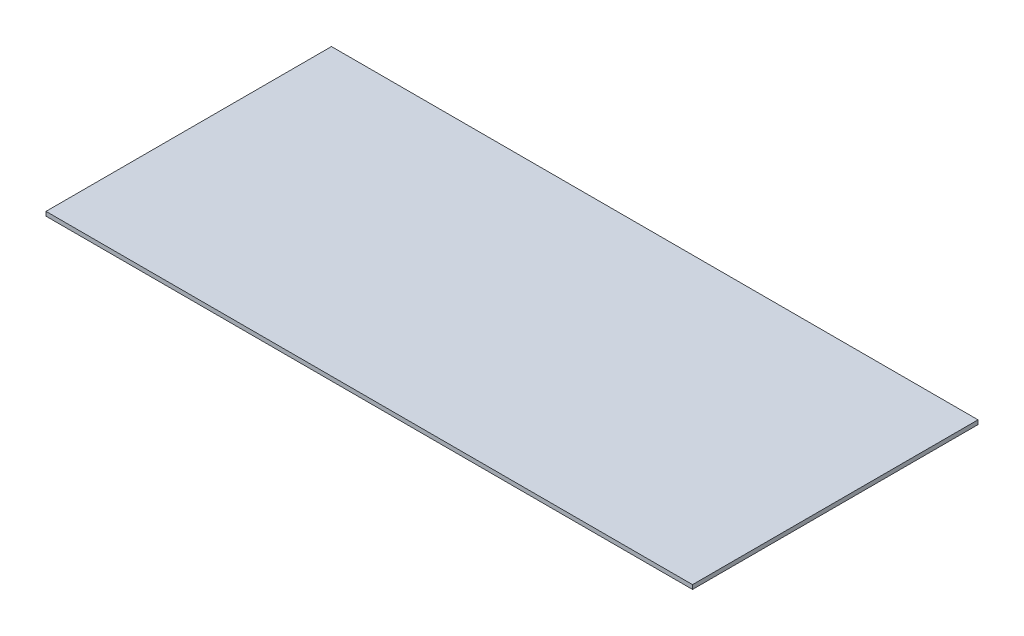
SolidWorks part; units mm, degrees
ref_plane "Front Plane" through (0, 0, 0) normal (0, 0, 1) x (1, 0, 0)
ref_plane "Top Plane" through (0, 0, 0) normal (0, 1, 0) x (1, 0, 0)
ref_plane "Right Plane" through (0, 0, 0) normal (1, 0, 0) x (0, 0, -1)
sketch "Sketch1" plane through (0, 0, 0) normal (0, 1, 0) x (1, 0, 0)
  line L1 (488.95, -215.9) -> (-488.95, -215.9)
  line L2 (488.95, -215.9) -> (488.95, 215.9)
  line L3 (488.95, 215.9) -> (-488.95, 215.9)
  line L4 (-488.95, -215.9) -> (-488.95, 215.9)
  line L5 (488.95, -215.9) -> (-488.95, 215.9) construction
  line L6 (488.95, 215.9) -> (-488.95, -215.9) construction
  point P0 (0, 0)
  dimension "D1" = 431.8
  dimension "D2" = 977.9
extrude "Glass" add sketch "Sketch1" along normal blind 6.35
